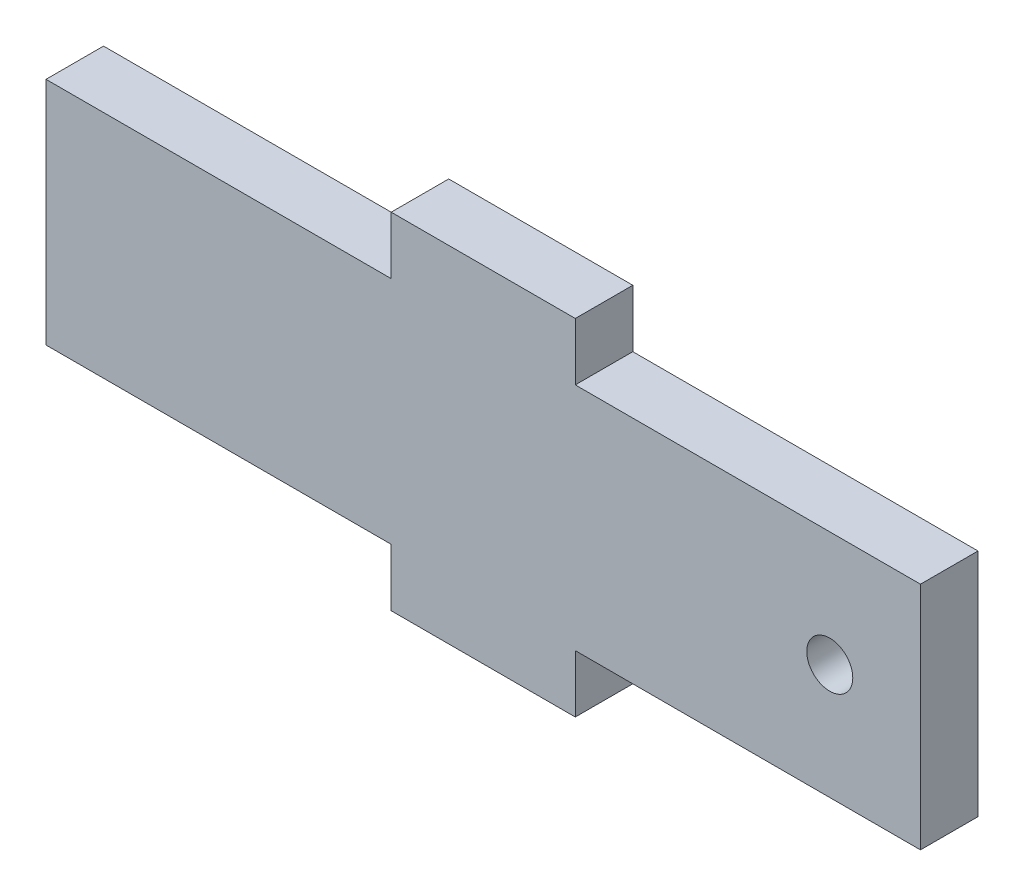
SolidWorks part; units mm, degrees
ref_plane "Front Plane" through (0, 0, 0) normal (0, 0, 1) x (1, 0, 0)
ref_plane "Top Plane" through (0, 0, 0) normal (0, 1, 0) x (1, 0, 0)
ref_plane "Right Plane" through (0, 0, 0) normal (1, 0, 0) x (0, 0, -1)
sketch "Sketch1" plane through (0, 0, 0) normal (0, 0, 1) x (1, 0, 0)
  line L0 (38, 0) -> (38.7368, 0) construction
  line L1 (0, 20.1053) -> (0, -22) construction
  line L2 (-8, 10) -> (-8, 15)
  line L3 (-38, 10) -> (-8, 10)
  line L4 (-38, 10) -> (-38, -10)
  line L5 (-38, -10) -> (-8, -10)
  line L6 (38, 10) -> (38, -10)
  line L7 (8, 10) -> (38, 10)
  line L8 (8, -10) -> (38, -10)
  line L9 (-8, 15) -> (8, 15)
  line L10 (8, 15) -> (8, 10)
  line L11 (-8, -10) -> (-8, -15)
  line L12 (-8, -15) -> (8, -15)
  line L13 (8, -15) -> (8, -10)
  line L14 (-7.646, 0) -> (32.8076, 0) construction
  circle A0 centre (30.1177, 0) radius 2
  point P5 (0, 0)
  dimension "D7" = 4
  dimension "D1" = 20
  dimension "D2" = 76
  dimension "D3" = 5
  dimension "D4" = 16
  dimension "D5" = 5
  dimension "D6" = 16
  dimension "D8" = 10
extrude "Boss-Extrude1" add sketch "Sketch1" along normal blind 5
